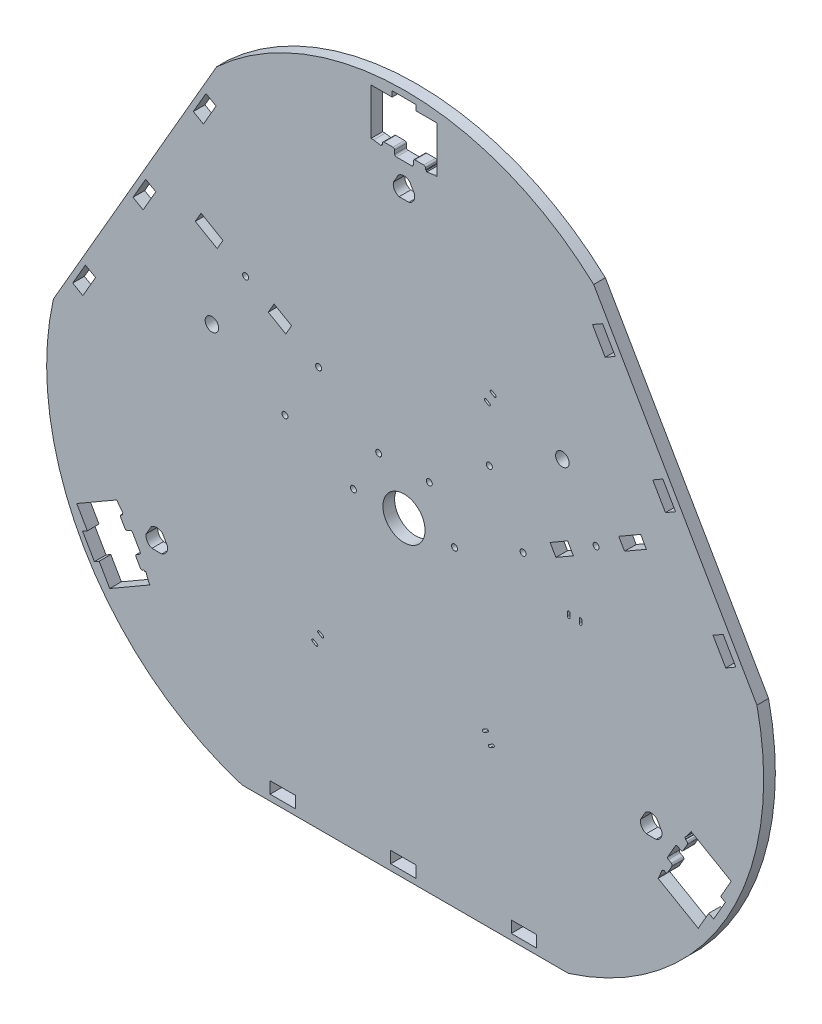
SolidWorks part; units mm, degrees
ref_plane "Front Plane" through (0, 0, 0) normal (0, 0, 1) x (1, 0, 0)
ref_plane "Top Plane" through (0, 0, 0) normal (0, 1, 0) x (1, 0, 0)
ref_plane "Right Plane" through (0, 0, 0) normal (1, 0, 0) x (0, 0, -1)
sketch "Sketch3" plane through (0, 0, 0) normal (0, 0, 1) x (1, 0, 0)
  line L0 (43.8498, 101.5258) -> (46.4748, 96.9792)
  line L1 (47.8409, 96.6131) -> (49.5729, 97.6131)
  line L2 (50.9389, 97.2471) -> (55.4389, 89.4529)
  line L3 (55.0729, 88.0869) -> (53.3409, 87.0869)
  line L4 (52.9748, 85.7208) -> (55.5998, 81.1742)
  line L5 (56.9659, 80.8082) -> (57.8319, 81.3082)
  line L6 (57.8319, 81.3082) -> (58.0819, 80.8752)
  line L7 (58.0819, 80.8752) -> (58.8211, 80.9948)
  line L8 (58.8211, 80.9948) -> (60.4869, 76.7096)
  line L9 (60.4869, 76.7096) -> (61.2369, 75.4105)
  line L10 (61.2369, 75.4105) -> (37.4212, 61.6605)
  line L11 (37.4212, 61.6605) -> (31.1412, 72.5378)
  line L12 (31.1412, 72.5378) -> (28.3266, 70.9128)
  line L13 (28.3266, 70.9128) -> (21.3266, 83.0372)
  line L14 (21.3266, 83.0372) -> (24.1412, 84.6622)
  line L15 (24.1412, 84.6622) -> (17.8612, 95.5395)
  line L16 (17.8612, 95.5395) -> (41.6769, 109.2895)
  line L17 (41.6769, 109.2895) -> (42.4269, 107.9904)
  line L18 (42.4269, 107.9904) -> (45.3051, 104.4052)
  line L19 (45.3051, 104.4052) -> (44.8319, 103.8248)
  line L20 (44.8319, 103.8248) -> (45.0819, 103.3918)
  line L21 (45.0819, 103.3918) -> (44.2159, 102.8918)
  line L22 (378.5577, 104.4052) -> (379.0309, 103.8248)
  line L23 (379.0309, 103.8248) -> (378.7809, 103.3918)
  line L24 (378.7809, 103.3918) -> (379.6469, 102.8918)
  line L25 (380.013, 101.5258) -> (377.388, 96.9792)
  line L26 (376.0219, 96.6131) -> (374.2899, 97.6131)
  line L27 (372.9239, 97.2471) -> (368.4239, 89.4529)
  line L28 (368.7899, 88.0869) -> (370.5219, 87.0869)
  line L29 (370.888, 85.7208) -> (368.263, 81.1742)
  line L30 (366.8969, 80.8082) -> (366.0309, 81.3082)
  line L31 (366.0309, 81.3082) -> (365.7809, 80.8752)
  line L32 (365.7809, 80.8752) -> (365.0417, 80.9948)
  line L33 (365.0417, 80.9948) -> (363.3759, 76.7096)
  line L34 (363.3759, 76.7096) -> (362.6259, 75.4105)
  line L35 (362.6259, 75.4105) -> (386.4416, 61.6605)
  line L36 (386.4416, 61.6605) -> (392.7216, 72.5378)
  line L37 (392.7216, 72.5378) -> (395.5362, 70.9128)
  line L38 (395.5362, 70.9128) -> (402.5362, 83.0372)
  line L39 (402.5362, 83.0372) -> (399.7216, 84.6622)
  line L40 (399.7216, 84.6622) -> (406.0016, 95.5395)
  line L41 (406.0016, 95.5395) -> (382.1859, 109.2895)
  line L42 (382.1859, 109.2895) -> (381.4359, 107.9904)
  line L43 (381.4359, 107.9904) -> (378.5577, 104.4052)
  line L44 (224.6814, 371.3) -> (224.6814, 370.3)
  line L45 (224.6814, 370.3) -> (225.1814, 370.3)
  line L46 (225.1814, 370.3) -> (225.4473, 369.6)
  line L47 (225.4473, 369.6) -> (229.9914, 370.3)
  line L48 (229.9914, 370.3) -> (231.4914, 370.3)
  line L49 (231.4914, 370.3) -> (231.4914, 397.8)
  line L50 (231.4914, 397.8) -> (218.9314, 397.8)
  line L51 (218.9314, 397.8) -> (218.9314, 401.05)
  line L52 (218.9314, 401.05) -> (204.9314, 401.05)
  line L53 (204.9314, 401.05) -> (204.9314, 397.8)
  line L54 (204.9314, 397.8) -> (192.3714, 397.8)
  line L55 (192.3714, 397.8) -> (192.3714, 370.3)
  line L56 (192.3714, 370.3) -> (193.8714, 370.3)
  line L57 (193.8714, 370.3) -> (198.4154, 369.6)
  line L58 (198.4154, 369.6) -> (198.6814, 370.3)
  line L59 (198.6814, 370.3) -> (199.1814, 370.3)
  line L60 (199.1814, 370.3) -> (199.1814, 371.3)
  line L61 (200.1814, 372.3) -> (205.4314, 372.3)
  line L62 (206.4314, 371.3) -> (206.4314, 369.3)
  line L63 (207.4314, 368.3) -> (216.4314, 368.3)
  line L64 (217.4314, 369.3) -> (217.4314, 371.3)
  line L65 (218.4314, 372.3) -> (223.6814, 372.3)
  line L66 (324.44, 361.3418) -> (421.2522, 193.6582)
  line L67 (309.4436, 0) -> (115.8192, 0)
  line L68 (4.0106, 193.6582) -> (100.8228, 361.3418)
  line L69 (101.1379, 268.1) -> (104.5679, 274.041)
  line L70 (104.5679, 274.041) -> (91.5775, 281.541)
  line L71 (91.5775, 281.541) -> (88.1475, 275.6)
  line L72 (88.1475, 275.6) -> (101.1379, 268.1)
  line L73 (23.0037, 220.6152) -> (15.4737, 207.5729)
  line L74 (15.4737, 207.5729) -> (21.4649, 204.1139)
  line L75 (21.4649, 204.1139) -> (28.9949, 217.1562)
  line L76 (28.9949, 217.1562) -> (23.0037, 220.6152)
  line L77 (58.7538, 282.5362) -> (51.2238, 269.4938)
  line L78 (51.2238, 269.4938) -> (57.215, 266.0348)
  line L79 (57.215, 266.0348) -> (64.745, 279.0772)
  line L80 (64.745, 279.0772) -> (58.7538, 282.5362)
  line L81 (94.5039, 344.4571) -> (86.9739, 331.4148)
  line L82 (86.9739, 331.4148) -> (92.965, 327.9558)
  line L83 (92.965, 327.9558) -> (100.495, 340.9981)
  line L84 (100.495, 340.9981) -> (94.5039, 344.4571)
  line L85 (337.2389, 330.8086) -> (329.7089, 343.8509)
  line L86 (329.7089, 343.8509) -> (323.7177, 340.3919)
  line L87 (323.7177, 340.3919) -> (331.2477, 327.3496)
  line L88 (331.2477, 327.3496) -> (337.2389, 330.8086)
  line L89 (372.989, 268.8876) -> (365.459, 281.93)
  line L90 (365.459, 281.93) -> (359.4678, 278.471)
  line L91 (359.4678, 278.471) -> (366.9978, 265.4286)
  line L92 (366.9978, 265.4286) -> (372.989, 268.8876)
  line L93 (408.7391, 206.9666) -> (401.2091, 220.009)
  line L94 (401.2091, 220.009) -> (395.2179, 216.55)
  line L95 (395.2179, 216.55) -> (402.7479, 203.5076)
  line L96 (402.7479, 203.5076) -> (408.7391, 206.9666)
  line L97 (275.5516, 3.5762) -> (290.6116, 3.5762)
  line L98 (290.6116, 3.5762) -> (290.6116, 10.4942)
  line L99 (290.6116, 10.4942) -> (275.5516, 10.4942)
  line L100 (275.5516, 10.4942) -> (275.5516, 3.5762)
  line L101 (204.0514, 3.5762) -> (219.1114, 3.5762)
  line L102 (219.1114, 3.5762) -> (219.1114, 10.4942)
  line L103 (219.1114, 10.4942) -> (204.0514, 10.4942)
  line L104 (204.0514, 10.4942) -> (204.0514, 3.5762)
  line L105 (147.6112, 10.4942) -> (132.5512, 10.4942)
  line L106 (132.5512, 10.4942) -> (132.5512, 3.5762)
  line L107 (132.5512, 3.5762) -> (147.6112, 3.5762)
  line L108 (147.6112, 3.5762) -> (147.6112, 10.4942)
  line L109 (141.8411, 244.6) -> (145.2711, 250.541)
  line L110 (145.2711, 250.541) -> (134.8788, 256.541)
  line L111 (134.8788, 256.541) -> (131.4488, 250.6)
  line L112 (131.4488, 250.6) -> (141.8411, 244.6)
  line L113 (218.19, 354.5349) -> (215.2857, 359.5654)
  line L114 (208.5771, 359.5654) -> (205.6728, 354.5349)
  line L115 (209.027, 348.7251) -> (214.8358, 348.7251)
  line L116 (68.6891, 105.6527) -> (71.5935, 100.6222)
  line L117 (68.2392, 94.8124) -> (62.4305, 94.8124)
  line L118 (59.0762, 100.6222) -> (61.9806, 105.6527)
  line L119 (355.6236, 94.8124) -> (361.4323, 94.8124)
  line L120 (364.7866, 100.6222) -> (361.8822, 105.6527)
  line L121 (355.1737, 105.6527) -> (352.2693, 100.6222)
  line L122 (298.5917, 215.9) -> (302.0217, 209.959)
  line L123 (302.0217, 209.959) -> (312.414, 215.959)
  line L124 (312.414, 215.959) -> (308.984, 221.9)
  line L125 (308.984, 221.9) -> (298.5917, 215.9)
  line L126 (342.7249, 233.459) -> (355.7153, 240.959)
  line L127 (355.7153, 240.959) -> (352.2853, 246.9)
  line L128 (352.2853, 246.9) -> (339.2949, 239.4)
  line L129 (339.2949, 239.4) -> (342.7249, 233.459)
  line L130 (161.0995, 100.6433) -> (163.1779, 99.4433)
  line L131 (163.9279, 100.7424) -> (161.8495, 101.9424)
  line L132 (157.5995, 94.5812) -> (159.6779, 93.3812)
  line L133 (160.4279, 94.6802) -> (158.3495, 95.8802)
  line L134 (259.5705, 98.7999) -> (261.6489, 99.9999)
  line L135 (260.8989, 101.299) -> (258.8205, 100.099)
  line L136 (263.0705, 92.7378) -> (265.1489, 93.9378)
  line L137 (264.3989, 95.2368) -> (262.3205, 94.0368)
  line L138 (310.4024, 183.1566) -> (310.4024, 185.5566)
  line L139 (308.9024, 185.5566) -> (308.9024, 183.1566)
  line L140 (317.4024, 183.1566) -> (317.4024, 185.5566)
  line L141 (315.9024, 185.5566) -> (315.9024, 183.1566)
  line L142 (262.7633, 269.3567) -> (260.6848, 270.5567)
  line L143 (259.9348, 269.2576) -> (262.0133, 268.0576)
  line L144 (266.2633, 275.4188) -> (264.1848, 276.6188)
  line L145 (263.4348, 275.3198) -> (265.5133, 274.1198)
  circle A0 centre (181.9314, 185) radius 1.775
  circle A1 centre (196.9314, 210.9808) radius 1.775
  circle A2 centre (118.0083, 262.3205) radius 1.775
  circle A3 centre (98.0083, 227.6795) radius 4
  circle A4 centre (161.3096, 237.3205) radius 1.775
  circle A5 centre (141.3096, 202.6795) radius 1.775
  circle A6 centre (211.9314, 185) radius 12.5
  circle A7 centre (226.9314, 210.9808) radius 1.775
  circle A8 centre (241.9314, 185) radius 1.775
  circle A9 centre (325.8544, 227.6795) radius 1.775
  circle A10 centre (305.8544, 262.3205) radius 4
  circle A11 centre (282.5532, 202.6795) radius 1.775
  circle A12 centre (262.5532, 237.3205) radius 1.775
  arc A13 (44.2159, 102.8918) -> (43.8498, 101.5258) centre (44.7159, 102.0258) ccw
  arc A14 (46.4748, 96.9792) -> (47.8409, 96.6131) centre (47.3409, 97.4792) ccw
  arc A15 (50.9389, 97.2471) -> (49.5729, 97.6131) centre (50.0729, 96.7471) ccw
  arc A16 (55.0729, 88.0869) -> (55.4389, 89.4529) centre (54.5729, 88.9529) ccw
  arc A17 (53.3409, 87.0869) -> (52.9748, 85.7208) centre (53.8409, 86.2208) ccw
  arc A18 (55.5998, 81.1742) -> (56.9659, 80.8082) centre (56.4659, 81.6742) ccw
  arc A19 (380.013, 101.5258) -> (379.6469, 102.8918) centre (379.1469, 102.0258) ccw
  arc A20 (376.0219, 96.6131) -> (377.388, 96.9792) centre (376.5219, 97.4792) ccw
  arc A21 (374.2899, 97.6131) -> (372.9239, 97.2471) centre (373.7899, 96.7471) ccw
  arc A22 (368.4239, 89.4529) -> (368.7899, 88.0869) centre (369.2899, 88.9529) ccw
  arc A23 (370.888, 85.7208) -> (370.5219, 87.0869) centre (370.0219, 86.2208) ccw
  arc A24 (366.8969, 80.8082) -> (368.263, 81.1742) centre (367.3969, 81.6742) ccw
  arc A25 (200.1814, 372.3) -> (199.1814, 371.3) centre (200.1814, 371.3) ccw
  arc A26 (206.4314, 371.3) -> (205.4314, 372.3) centre (205.4314, 371.3) ccw
  arc A27 (206.4314, 369.3) -> (207.4314, 368.3) centre (207.4314, 369.3) ccw
  arc A28 (216.4314, 368.3) -> (217.4314, 369.3) centre (216.4314, 369.3) ccw
  arc A29 (218.4314, 372.3) -> (217.4314, 371.3) centre (218.4314, 371.3) ccw
  arc A30 (224.6814, 371.3) -> (223.6814, 372.3) centre (223.6814, 371.3) ccw
  arc A31 (324.44, 361.3418) -> (100.8228, 361.3418) centre (212.6314, 240) ccw
  arc A32 (309.4436, 0) -> (421.2522, 193.6582) centre (260.2628, 157.5) ccw
  arc A33 (4.0106, 193.6582) -> (115.8192, 0) centre (165, 157.5) ccw
  arc A34 (215.2857, 359.5654) -> (208.5771, 359.5654) centre (211.9314, 355.9251) ccw
  arc A35 (205.6728, 354.5349) -> (209.027, 348.7251) centre (210.5025, 353.4501) ccw
  arc A36 (214.8358, 348.7251) -> (218.19, 354.5349) centre (213.3603, 353.4501) ccw
  arc A37 (68.2392, 94.8124) -> (71.5935, 100.6222) centre (66.7638, 99.5374) ccw
  arc A38 (59.0762, 100.6222) -> (62.4305, 94.8124) centre (63.9059, 99.5374) ccw
  arc A39 (68.6891, 105.6527) -> (61.9806, 105.6527) centre (65.3348, 102.0124) ccw
  arc A40 (361.4323, 94.8124) -> (364.7866, 100.6222) centre (359.9569, 99.5374) ccw
  arc A41 (361.8822, 105.6527) -> (355.1737, 105.6527) centre (358.528, 102.0124) ccw
  arc A42 (352.2693, 100.6222) -> (355.6236, 94.8124) centre (357.099, 99.5374) ccw
  arc A43 (163.1779, 99.4433) -> (163.9279, 100.7424) centre (163.5529, 100.0929) ccw
  arc A44 (161.8495, 101.9424) -> (161.0995, 100.6433) centre (161.4745, 101.2929) ccw
  arc A45 (159.6779, 93.3812) -> (160.4279, 94.6802) centre (160.0529, 94.0307) ccw
  arc A46 (158.3495, 95.8802) -> (157.5995, 94.5812) centre (157.9745, 95.2307) ccw
  arc A47 (261.6489, 99.9999) -> (260.8989, 101.299) centre (261.2739, 100.6495) ccw
  arc A48 (258.8205, 100.099) -> (259.5705, 98.7999) centre (259.1955, 99.4495) ccw
  arc A49 (265.1489, 93.9378) -> (264.3989, 95.2368) centre (264.7739, 94.5873) ccw
  arc A50 (262.3205, 94.0368) -> (263.0705, 92.7378) centre (262.6955, 93.3873) ccw
  arc A51 (310.4024, 185.5566) -> (308.9024, 185.5566) centre (309.6524, 185.5566) ccw
  arc A52 (308.9024, 183.1566) -> (310.4024, 183.1566) centre (309.6524, 183.1566) ccw
  arc A53 (317.4024, 185.5566) -> (315.9024, 185.5566) centre (316.6524, 185.5566) ccw
  arc A54 (315.9024, 183.1566) -> (317.4024, 183.1566) centre (316.6524, 183.1566) ccw
  arc A55 (260.6848, 270.5567) -> (259.9348, 269.2576) centre (260.3098, 269.9071) ccw
  arc A56 (262.0133, 268.0576) -> (262.7633, 269.3567) centre (262.3883, 268.7071) ccw
  arc A57 (264.1848, 276.6188) -> (263.4348, 275.3198) centre (263.8098, 275.9693) ccw
  arc A58 (265.5133, 274.1198) -> (266.2633, 275.4188) centre (265.8883, 274.7693) ccw
  dimension "D1" = 6.918
extrude "Boss-Extrude1" add sketch "Sketch3" along normal blind 6.92
